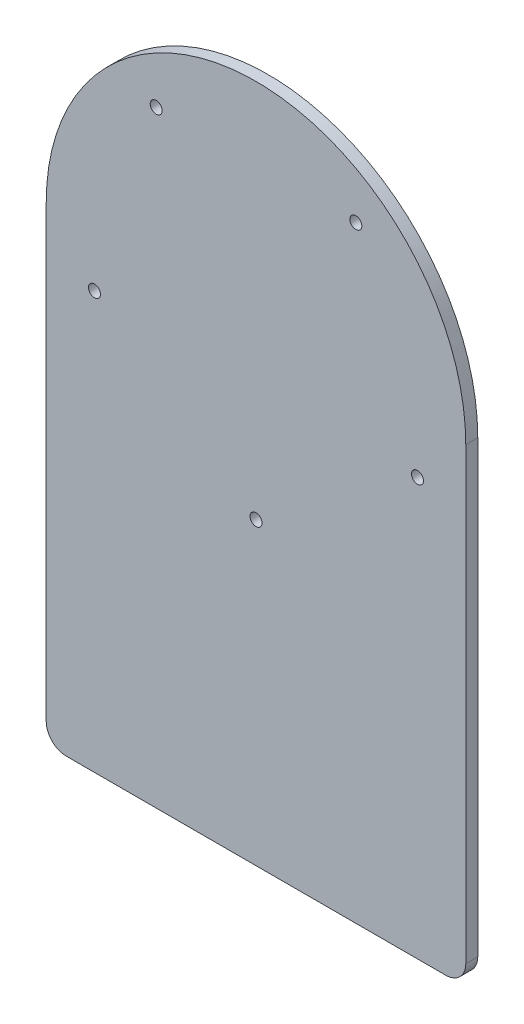
SolidWorks part; units mm, degrees
ref_plane "Alzado" through (0, 0, 0) normal (0, 0, 1) x (1, 0, 0)
ref_plane "Planta" through (0, 0, 0) normal (0, 1, 0) x (1, 0, 0)
ref_plane "Vista lateral" through (0, 0, 0) normal (1, 0, 0) x (0, 0, -1)
sketch "Croquis1" plane through (0, 0, 0) normal (0, 0, 1) x (1, 0, 0)
  line L1 (-52.5, 0) -> (52.5, 0)
  line L2 (-52.5, 0) -> (-52.5, -117.5)
  line L3 (-52.5, -117.5) -> (52.5, -117.5)
  line L4 (52.5, 0) -> (52.5, -117.5)
  circle A0 centre (0, 0) radius 52.5
  point P7 (0, -117.5)
  point P8 (0, 52.5)
  dimension "D1" = 170
  dimension "D2" = 105
extrude "Saliente-Extruir1" add sketch "Croquis1" along normal blind 3 contours A0 L2 L3 L4 | L1 A0 | L1 A0
fillet "Redondeo1" radius 5 2 edges at (52.5, -117.5, 1.5) (-52.5, -117.5, 1.5)
sketch "Croquis2" plane through (0, 0, 3) normal (0, 0, 1) x (1, 0, 0)
  circle A0 centre (0, 0) radius 42.5 construction
  circle A1 centre (0, -42.5) radius 1.5
  circle A2 centre (-40.4199, -13.1332) radius 1.5
  circle A3 centre (-24.9809, 34.3832) radius 1.5
  circle A4 centre (24.9809, 34.3832) radius 1.5
  circle A5 centre (40.4199, -13.1332) radius 1.5
  point P5 (0, 0)
  point P6 (25.2418, 34.1922)
  point P7 (40.8946, -14.7738)
  point P16 (0, 0)
  dimension "D1" = 85
  dimension "D2" = 3
  dimension "D3" = 5
extrude "Cortar-Extruir1" cut sketch "Croquis2" against normal blind 3
